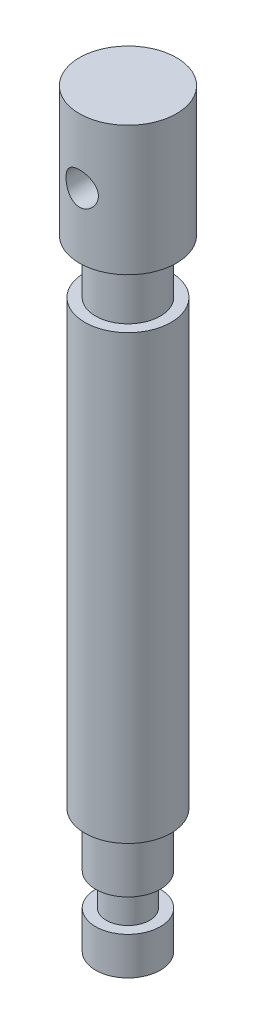
SolidWorks part; units mm, degrees
ref_plane "Front Plane" through (0, 0, 0) normal (0, 0, 1) x (1, 0, 0)
ref_plane "Top Plane" through (0, 0, 0) normal (0, 1, 0) x (1, 0, 0)
ref_plane "Right Plane" through (0, 0, 0) normal (1, 0, 0) x (0, 0, -1)
sketch "Sketch1" plane through (0, 0, 0) normal (0, 1, 0) x (1, 0, 0)
  circle A0 centre (0, 0) radius 8
  dimension "D1" = 16
extrude "Boss-Extrude1" add sketch "Sketch1" along normal blind 82
sketch "Sketch2" plane through (0, 82, 0) normal (0, 1, 0) x (1, 0, 0)
  circle A0 centre (0, 0) radius 6
  dimension "D1" = 12
extrude "Boss-Extrude2" add sketch "Sketch2" along normal blind 10
sketch "Sketch4" plane through (0, 92, 0) normal (0, 1, 0) x (1, 0, 0)
  circle A0 centre (0, 0) radius 9
  dimension "D1" = 18
extrude "Boss-Extrude3" add sketch "Sketch4" along normal blind 24
sketch "Sketch5" plane through (0, 0, 0) normal (0, -1, 0) x (1, 0, 0)
  circle A0 centre (0, 0) radius 6
  dimension "D1" = 12
extrude "Boss-Extrude4" add sketch "Sketch5" along normal blind 10
sketch "Sketch6" plane through (0, -10, 0) normal (0, -1, 0) x (1, 0, 0)
  circle A0 centre (0, 0) radius 4
  dimension "D1" = 8
extrude "Boss-Extrude5" add sketch "Sketch6" along normal blind 6
sketch "Sketch7" plane through (0, -16, 0) normal (0, -1, 0) x (1, 0, 0)
  circle A0 centre (0, 0) radius 6
  dimension "D1" = 12
extrude "Boss-Extrude6" add sketch "Sketch7" along normal blind 7
sketch "Sketch8" plane through (0, 0, 0) normal (0, 0, 1) x (1, 0, 0)
  line L0 (9, 116) -> (-9, 116) construction
  circle A0 centre (0, 104) radius 3
  dimension "D1" = 6
  dimension "D2" = 12
extrude "Cut-Extrude2" cut sketch "Sketch8" against normal through all both and the other way through all
